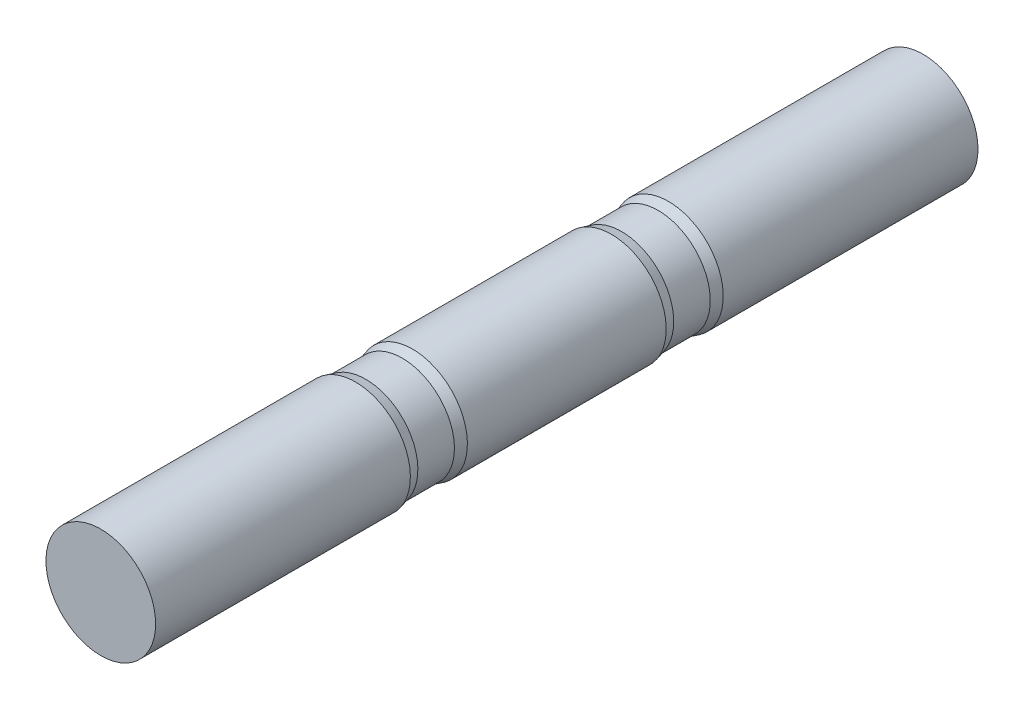
SolidWorks part; units mm, degrees
material "Plain Carbon Steel"
ref_plane "Front Plane" through (0, 0, 0) normal (0, 0, 1) x (1, 0, 0)
ref_plane "Top Plane" through (0, 0, 0) normal (0, 1, 0) x (1, 0, 0)
ref_plane "Right Plane" through (0, 0, 0) normal (1, 0, 0) x (0, 0, -1)
sketch "Sketch1" plane through (0, 0, 0) normal (0, 0, 1) x (1, 0, 0)
  circle A0 centre (0, 0) radius 30
  dimension "D1" = 60
extrude "Boss-Extrude1" add sketch "Sketch1" along normal mid plane 450
sketch "Sketch2" plane through (0, 0, 0) normal (1, 0, 0) x (0, 0, -1)
  line L0 (-225, 0) -> (225, 0) construction
  line L1 (-225, 30) -> (-225, -30) construction
  line L2 (225, -30) -> (225, 30) construction
  line L3 (0, 0) -> (0, 30) construction
  line L4 (225, 30) -> (-225, 30) construction
  circle A0 centre (72, 0) radius 7
  circle A1 centre (-72, 0) radius 7
  dimension "D1" = 14
  dimension "D2" = 72
extrude "Cut-Extrude1" [suppressed] cut sketch "Sketch2" against normal through all and the other way through all
sketch "Sketch3" plane through (0, 0, 0) normal (1, 0, 0) x (0, 0, -1)
  line L0 (-225, 0) -> (225, 0) construction
  line L1 (-225, 30) -> (-225, -30) construction
  line L2 (225, -30) -> (225, 30) construction
  line L3 (0, 30) -> (0, -30) construction
  line L4 (225, 30) -> (-225, 30) construction
  line L5 (-225, -30) -> (225, -30) construction
  line L6 (-85.5981, 30) -> (-80, 28.5)
  line L7 (-80, 28.5) -> (-60, 28.5)
  line L8 (-60, 28.5) -> (-54.4019, 30)
  line L9 (-85.5981, 30) -> (-54.4019, 30)
  line L10 (-70, 30) -> (-70, 28.5) construction
  line L11 (-90, 0) -> (-90, 30) construction
  line L12 (70, 30) -> (70, 28.5) construction
  line L13 (85.5981, 30) -> (54.4019, 30)
  line L14 (60, 28.5) -> (54.4019, 30)
  line L15 (80, 28.5) -> (60, 28.5)
  line L16 (85.5981, 30) -> (80, 28.5)
  dimension "D1" = 1.5
  dimension "D2" = 20
  dimension "D3" = 165
  dimension "D4" = 165
  dimension "D5" = 20
  dimension "D6" = 90
  dimension "D7" = 30
revolve "Cut-Revolve1" cut sketch "Sketch3" angle 360 about L0
